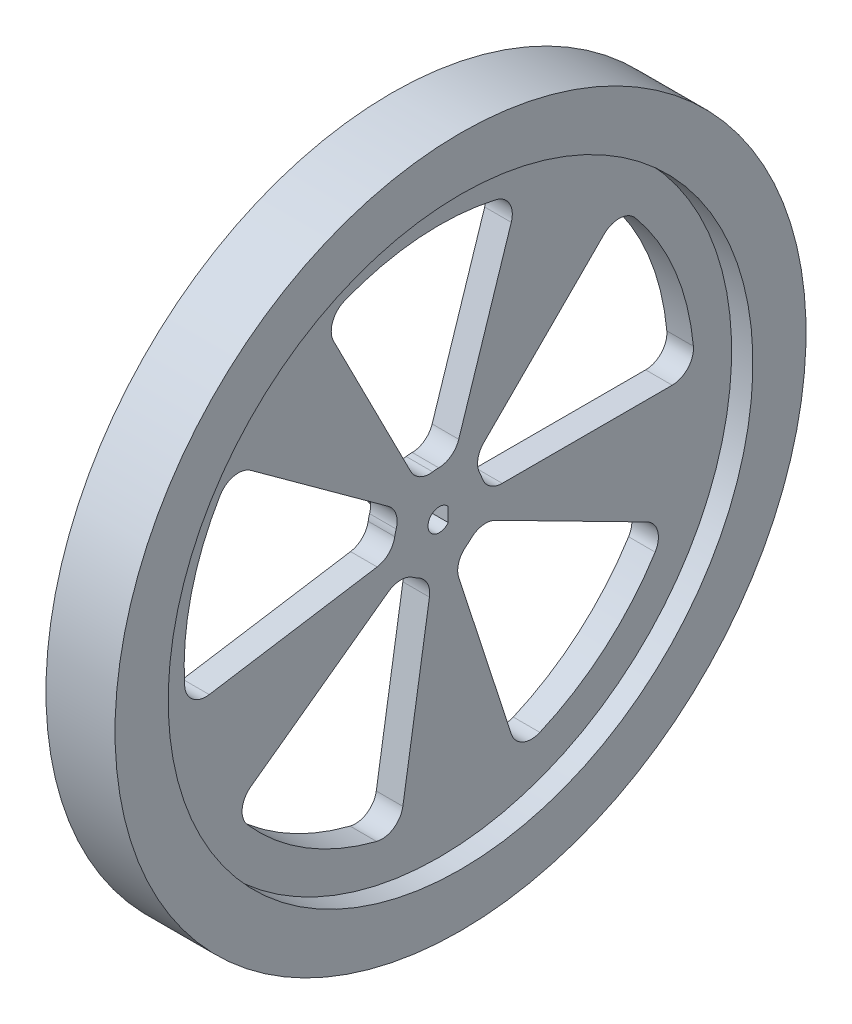
SolidWorks part; units mm, degrees
material "ABS"
ref_plane "Front Plane" through (0, 0, 0) normal (0, 0, 1) x (1, 0, 0)
ref_plane "Top Plane" through (0, 0, 0) normal (0, 1, 0) x (1, 0, 0)
ref_plane "Right Plane" through (0, 0, 0) normal (1, 0, 0) x (0, 0, -1)
sketch "Sketch3" plane through (0, 0, 0) normal (0, 0, 1) x (1, 0, 0)
  line L1 (-2.5, 0) -> (2.5, 0)
  line L5 (2.5, 0) -> (2.5, 55)
  line L6 (-2.5, 0) -> (-2.5, 55)
  line L12 (0, 0) -> (0, 43) construction
  line L13 (-6.5, 55) -> (-2.5, 55)
  line L15 (-6.5, 65) -> (-6.5, 55)
  line L17 (6.5, 65) -> (6.5, 55)
  line L18 (2.5, 55) -> (6.5, 55)
  line L19 (6.5, 65) -> (-6.5, 65)
  line L20 (2.5, 55) -> (0, 55) construction
  line L21 (0, 55) -> (-2.5, 55) construction
  dimension "D1" = 2.5
  dimension "D3" = 4
  dimension "D4" = 10
  dimension "D5" = 65
revolve "Shape_Roue" add sketch "Sketch3" angle 360 about L1
sketch "Sketch6" plane through (2.5, 0, 0) normal (1, 0, 0) x (0, 0, -1)
  line L0 (8.3741, 8.3741) -> (30.9839, 30.9839)
  line L1 (43.8178, 0) -> (11.8427, 0)
  line L2 (0, 0) -> (24.1309, 0) construction
  line L3 (0, 0) -> (0, 5.2799) construction
  line L4 (48, 0) -> (0, 0) construction
  line L5 (33.9411, 33.9411) -> (0, 0) construction
  line L6 (7.853, 3.2528) -> (0, 0) construction
  line L7 (7.853, 3.2528) -> (44.3462, 18.3688) construction
  line L8 (44.3462, 18.3688) -> (50.8134, 21.0476) construction
  circle A0 centre (0, 0) radius 55 construction
  arc A1 (8.3741, 8.3741) -> (7.6177, 3.771) centre (11.2025, 5.5456) ccw
  arc A2 (7.6177, 3.771) -> (8.053, 2.72) centre (0, 0) cw
  arc A3 (36.8861, 30.715) -> (47.8012, 4.3636) centre (0, 0) cw
  arc A5 (11.8427, 0) -> (8.053, 2.72) centre (11.8427, 4) cw
  arc A6 (43.8178, 0) -> (47.8012, 4.3636) centre (43.8178, 4) ccw
  arc A7 (30.9839, 30.9839) -> (36.8861, 30.715) centre (33.8123, 28.1554) cw
  circle A9 centre (0, 0) radius 55 construction
  dimension "D1" = 45
  dimension "D3" = 7
  dimension "D5" = 4
  dimension "D2" = 8.5
extrude "Cut-Extrude1" cut sketch "Sketch6" along direction (-1, 0, 0) on the side against the normal up to next (5 mm away)
pattern_circular "CirPattern1" count 5 over 360 about axis through (0, 0, 0) along (1, 0, 0) of "Cut-Extrude1"
sketch "Sketch8" plane through (-2.5, 0, 0) normal (1, 0, 0) x (0, 0, -1)
  line L0 (0, 0) -> (2.75, 0) construction
  circle A0 centre (0, 0) radius 2.75
  dimension "D1" = 2.75
extrude "Boss-Extrude1" add sketch "Sketch8" against normal blind 6
sketch "Sketch7" plane through (2.5, 0, 0) normal (1, 0, 0) x (0, 0, -1)
  line L0 (0, 0) -> (1.9231, 0) construction
  line L1 (0, -2.125) -> (0, 2.125) construction
  line L2 (0, 0) -> (-2.125, 0)
  line L3 (1.675, 1.3077) -> (1.675, -1.3077)
  arc A0 (1.675, 1.3077) -> (1.675, -1.3077) centre (0, 0) ccw
  dimension "D1" = 4.25
  dimension "D2" = 3.8
extrude "Cut-Extrude2" cut sketch "Sketch7" against normal up to next
